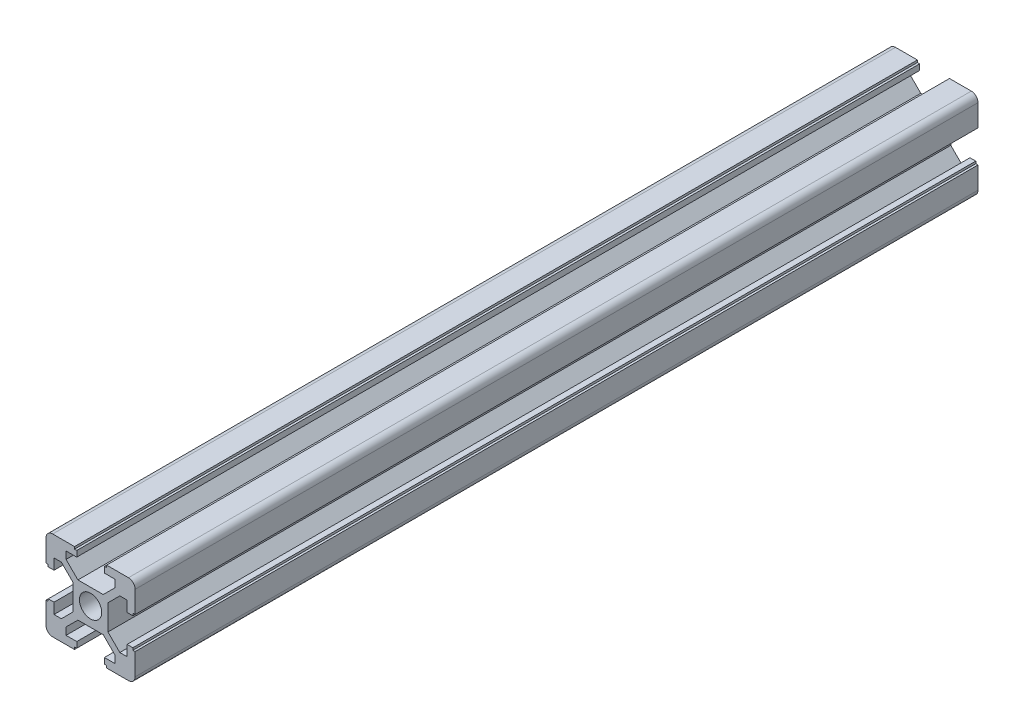
SolidWorks part; units mm, degrees
ref_plane "Front Plane" through (0, 0, 0) normal (0, 0, 1) x (1, 0, 0)
ref_plane "Top Plane" through (0, 0, 0) normal (0, 1, 0) x (1, 0, 0)
ref_plane "Right Plane" through (0, 0, 0) normal (1, 0, 0) x (0, 0, -1)
sketch "Sketch1" plane through (0, 0, 0) normal (0, 0, 1) x (1, 0, 0)
  line L0 (0, 13.3843) -> (0, -12.9126) construction
  line L1 (-14.4653, 0) -> (14.4653, 0) construction
  line L2 (2.8393, 3.9) -> (5.5, 6.5607)
  line L3 (-8.5, 10) -> (-3.6, 10)
  line L4 (-10, 8.5) -> (-10, 3.6)
  line L5 (-8.5, -10) -> (-3.6, -10)
  line L6 (10, 8.5) -> (10, 3.6)
  line L7 (-10, 10) -> (10, -10) construction
  line L8 (-10, -10) -> (10, 10) construction
  line L9 (-5.5, 8.2) -> (-3.1, 8.2)
  line L10 (-5.9626, 4.902) -> (-4.902, 5.9626) construction
  line L11 (-2.8393, 3.9) -> (-5.5, 6.5607)
  line L12 (-5.5, 8.2) -> (-5.5, 6.5607)
  line L13 (-2.8393, 3.9) -> (2.8393, 3.9)
  line L14 (5.5, 8.2) -> (5.5, 6.5607)
  line L15 (-3.1, 9.5) -> (-3.1, 8.2)
  line L16 (3.1, 9.5) -> (3.1, 8.2)
  line L17 (-3.1, 9.5) -> (3.1, 9.5) construction
  line L18 (-3.1, 9.5) -> (-3.6, 9.5)
  line L19 (-3.6, 9.5) -> (-3.6, 10)
  line L20 (3.1, 9.5) -> (3.6, 9.5)
  line L21 (3.6, 9.5) -> (3.6, 10)
  line L22 (3.6, 10) -> (8.5, 10)
  line L23 (3.1, 8.2) -> (5.5, 8.2)
  line L24 (-9.5, -3.1) -> (-9.5, -3.6)
  line L25 (-9.5, -3.6) -> (-10, -3.6)
  line L26 (-9.5, -3.1) -> (-8.2, -3.1)
  line L27 (-8.2, -3.1) -> (-8.2, -5.5)
  line L28 (-8.2, -5.5) -> (-6.5607, -5.5)
  line L29 (-3.9, -2.8393) -> (-6.5607, -5.5)
  line L30 (-3.9, 2.8393) -> (-3.9, -2.8393)
  line L31 (-3.9, 2.8393) -> (-6.5607, 5.5)
  line L32 (-8.2, 5.5) -> (-6.5607, 5.5)
  line L33 (-8.2, 5.5) -> (-8.2, 3.1)
  line L34 (-9.5, 3.1) -> (-8.2, 3.1)
  line L35 (-9.5, 3.1) -> (-9.5, 3.6)
  line L36 (-9.5, 3.6) -> (-10, 3.6)
  line L37 (-3.6, -9.5) -> (-3.6, -10)
  line L38 (-3.1, -9.5) -> (-3.6, -9.5)
  line L39 (-3.1, -9.5) -> (-3.1, -8.2)
  line L40 (-3.1, -8.2) -> (-5.5, -8.2)
  line L41 (-5.5, -8.2) -> (-5.5, -6.5607)
  line L42 (-2.8393, -3.9) -> (-5.5, -6.5607)
  line L43 (2.8393, -3.9) -> (-2.8393, -3.9)
  line L44 (2.8393, -3.9) -> (5.5, -6.5607)
  line L45 (5.5, -8.2) -> (5.5, -6.5607)
  line L46 (5.5, -8.2) -> (3.1, -8.2)
  line L47 (3.1, -9.5) -> (3.6, -9.5)
  line L48 (3.1, -9.5) -> (3.1, -8.2)
  line L49 (3.6, -9.5) -> (3.6, -10)
  line L50 (9.5, -3.6) -> (10, -3.6)
  line L51 (9.5, -3.1) -> (9.5, -3.6)
  line L52 (9.5, -3.1) -> (8.2, -3.1)
  line L53 (8.2, -5.5) -> (8.2, -3.1)
  line L54 (8.2, -5.5) -> (6.5607, -5.5)
  line L55 (3.9, -2.8393) -> (6.5607, -5.5)
  line L56 (3.9, -2.8393) -> (3.9, 2.8393)
  line L57 (3.9, 2.8393) -> (6.5607, 5.5)
  line L58 (8.2, 5.5) -> (6.5607, 5.5)
  line L59 (8.2, 3.1) -> (8.2, 5.5)
  line L60 (9.5, 3.1) -> (8.2, 3.1)
  line L61 (9.5, 3.1) -> (9.5, 3.6)
  line L62 (9.5, 3.6) -> (10, 3.6)
  line L63 (-10, -3.6) -> (-10, -8.5)
  line L64 (3.6, -10) -> (8.5, -10)
  line L65 (10, -3.6) -> (10, -8.5)
  arc A0 (8.5, 10) -> (10, 8.5) centre (8.5, 8.5) cw
  arc A1 (8.5, -10) -> (10, -8.5) centre (8.5, -8.5) ccw
  arc A2 (-10, -8.5) -> (-8.5, -10) centre (-8.5, -8.5) ccw
  arc A3 (-8.5, 10) -> (-10, 8.5) centre (-8.5, 8.5) ccw
  circle A4 centre (0, 0.2358) radius 2.5
  point P5 (0, 0)
  point P30 (-5.4323, 5.4323)
  point P38 (0, 9.5)
  dimension "D3" = 1.5
  dimension "D15" = 5
  dimension "D1" = 20
  dimension "D2" = 20
  dimension "D4" = 6.2
  dimension "D5" = 11
  dimension "D6" = 1.8
  dimension "D7" = 1.5
  dimension "D8" = 90
  dimension "D9" = 0.5
  dimension "D10" = 0.5
  dimension "D11" = 0.5
  dimension "D12" = 0.5
  dimension "D13" = 6.1
  dimension "D14" = 45
extrude "Boss-Extrude1" add sketch "Sketch1" along normal blind 189.0961
scale "缩放比例1" bodies to scale 101 scale about centroid uniform scaling yes scale factor 1
scale "缩放比例2" scale about centroid uniform scaling yes scale factor 3
scale "缩放比例3" scale about centroid uniform scaling yes scale factor 6
scale "缩放比例5" scale about centroid uniform scaling yes scale factor 2
scale "缩放比例6" scale about centroid uniform scaling yes scale factor 0.25
scale "缩放比例7" scale about centroid uniform scaling yes scale factor 0.125
scale "缩放比例8" scale about centroid uniform scaling yes scale factor 0.25
scale "缩放比例9" scale about centroid uniform scaling yes scale factor 4
scale "缩放比例10" scale about centroid uniform scaling yes scale factor 4
sketch "草图5" plane through (0, -44.9052, 0) normal (0, -1, 0) x (-1, 0, 0)
  circle A0 centre (26.2054, 311.8546) radius 5.1526
